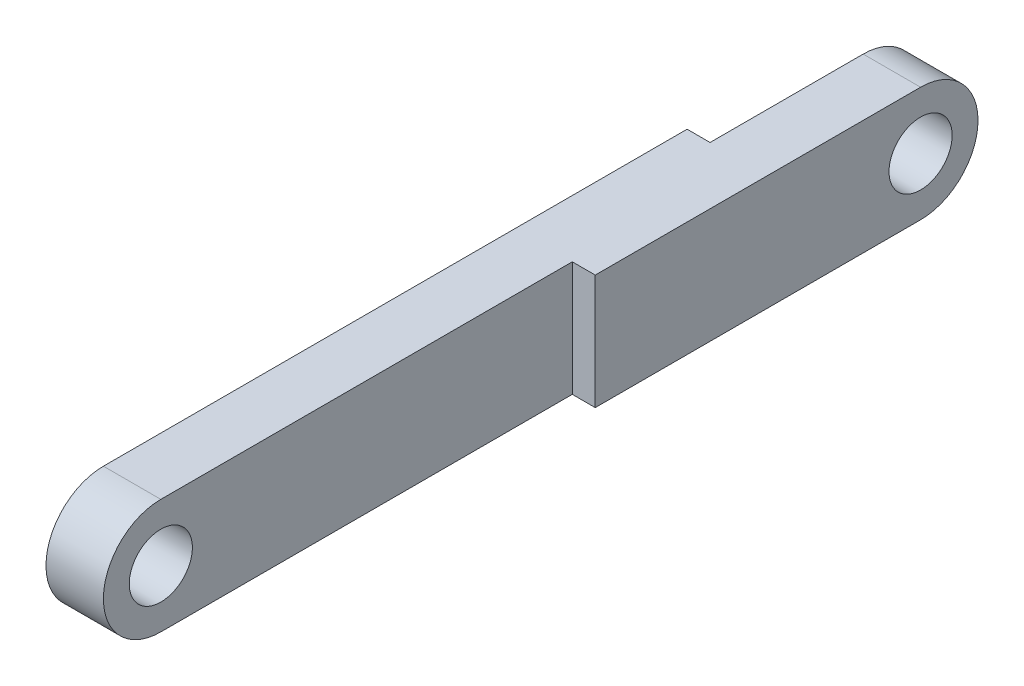
SolidWorks part; units mm, degrees
material "Plain Carbon Steel"
ref_plane "Front Plane" through (0, 0, 0) normal (0, 0, 1) x (1, 0, 0)
ref_plane "Top Plane" through (0, 0, 0) normal (0, 1, 0) x (1, 0, 0)
ref_plane "Right Plane" through (0, 0, 0) normal (1, 0, 0) x (0, 0, -1)
sketch "Sketch1" plane through (0, 0, 0) normal (1, 0, 0) x (0, 0, -1)
  line L24 (0, 3) -> (38.5, 3)
  line L25 (0, -3) -> (38.5, -3)
  arc A6 (0, 3) -> (0, -3) centre (0, 0) ccw
  arc A8 (38.5, 3) -> (38.5, -3) centre (38.5, 0) cw
  circle A10 centre (0, 0) radius 1.65
  circle A11 centre (38.5, 0) radius 1.65
  dimension "D1" = 6
  dimension "D2" = 38.5
  dimension "D3" = 3.3
extrude "Boss-Extrude1" add sketch "Sketch1" along normal blind 3
sketch "Sketch3" plane through (0, 0, 0) normal (-1, 0, 0) x (0, 0, 1)
  line L0 (-41.5, 3) -> (-30.5, 3)
  line L1 (-38.5, 3) -> (0, 3) construction
  line L2 (-30.5, 3) -> (-30.5, -3)
  line L3 (0, -3) -> (-38.5, -3) construction
  line L4 (-30.5, -3) -> (-41.5, -3)
  line L5 (-41.5, -3) -> (-41.5, 3)
  arc A1 (-38.5, 3) -> (-38.5, -3) centre (-38.5, 0) ccw construction
  dimension "D1" = 11
extrude "Cut-Extrude2" cut sketch "Sketch3" against normal blind 1.2
sketch "Sketch4" plane through (3, 0, 0) normal (1, 0, 0) x (0, 0, -1)
  line L0 (21.5, 3) -> (21.5, -3)
  line L5 (0, -3) -> (38.5, -3)
  line L6 (38.5, 3) -> (0, 3)
  line L7 (0, -3) -> (21.5, -3)
  line L8 (21.5, 3) -> (0, 3)
  arc A1 (38.5, -3) -> (38.5, 3) centre (38.5, 0) ccw construction
  arc A2 (0, 3) -> (0, -3) centre (0, 0) ccw
  arc A3 (38.5, -3) -> (38.5, 3) centre (38.5, 0) ccw
  arc A4 (0, 3) -> (0, -3) centre (0, 0) ccw
  circle M1 centre (38.5, 0) radius 1.65
  line M3 (0, -3) -> (38.5, -3)
  arc M4 (38.5, -3) -> (38.5, 3) centre (38.5, 0) ccw
  line M5 (38.5, 3) -> (0, 3)
  dimension "D2" = 17
  dimension "D1" = 0
extrude "Boss-Extrude2" add sketch "Sketch4" along normal blind 1.2 contours L0 M5 M3 M4 M1
